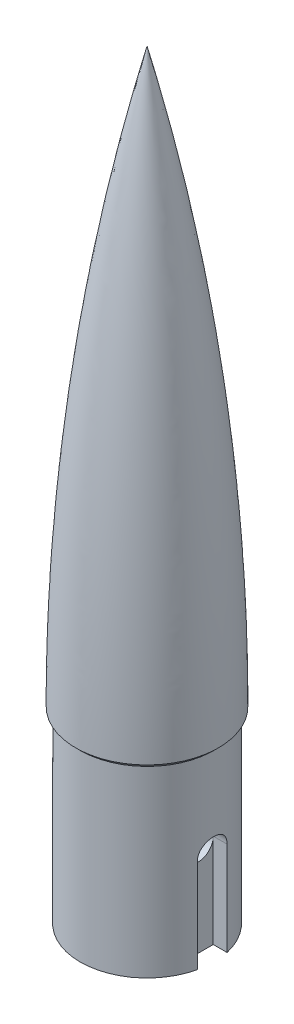
SolidWorks part; units mm, degrees
ref_plane "Front Plane" through (0, 0, 0) normal (0, 0, 1) x (1, 0, 0)
ref_plane "Top Plane" through (0, 0, 0) normal (0, 1, 0) x (1, 0, 0)
ref_plane "Right Plane" through (0, 0, 0) normal (1, 0, 0) x (0, 0, -1)
sketch "Sketch1" plane through (0, 0, 0) normal (0, 1, 0) x (1, 0, 0)
  circle A0 centre (0, 0) radius 8.895
  dimension "D1" = 17.79
extrude "Boss-Extrude1" add sketch "Sketch1" against normal blind 25
sketch "Sketch2" plane through (0, -25, 0) normal (0, -1, 0) x (1, 0, 0)
  line L0 (-6.8312, 1.9844) -> (-6.8312, -1.9844)
  line L1 (-6.8312, 1.9844) -> (-8.6708, 1.9844)
  line L2 (-6.8312, -1.9844) -> (-8.6708, -1.9844)
  line L3 (-8.895, 0) -> (-8.895, -1.1975) construction
  circle A0 centre (0, 0) radius 8.895 construction
  arc A1 (-8.6708, 1.9844) -> (-8.6708, -1.9844) centre (0, 0) ccw
  point P3 (-6.8313, 0)
  dimension "D2" = 3.9688
  dimension "D1" = 2.0637
extrude "Cut-Extrude1" cut sketch "Sketch2" against normal blind 12.5
mirror "Mirror1" about plane through (0, 0, 0) normal (1, 0, 0) of "Cut-Extrude1"
sketch "Sketch3" plane through (0, 0, 0) normal (1, 0, 0) x (0, 0, -1)
  line L0 (1.9844, -12.5) -> (-1.9844, -12.5) construction
  circle A0 centre (0, -12.5) radius 1.9844
extrude "Cut-Extrude2" cut sketch "Sketch3" against normal through all both and the other way through all
sketch "Sketch4" plane through (0, 0, 0) normal (0, 0, 1) x (1, 0, 0)
  line L0 (0, 0) -> (0, 76.2)
  line L1 (0, 0) -> (9.5, 0)
  arc A0 (9.5, 0) -> (0, 76.2) centre (-300.8521, 0) ccw
  dimension "D1" = 9.5
  dimension "D2" = 76.2
revolve "Revolve1" add sketch "Sketch4" angle 360 about L0
chamfer "Chamfer1" distance 0.6 angle 45 1 edges at (0, 0, 8.895)
equation "\"D_SHOULDER\"= 17.79mm"
equation "\"OD_AIRF\"= 19mm"
equation "\"W_CORD\"= 3.175mm"
equation "\"L_SHOULDER\"= 25mm"
equation "\"L_CONE\"= 3in"
equation "\"D1@Sketch1\"=\"D_SHOULDER\""
equation "\"D1@Boss-Extrude1\"=\"L_SHOULDER\""
equation "\"D2@Sketch2\"=1.25*\"W_CORD\""
equation "\"D1@Sketch2\"=0.65*\"W_CORD\""
equation "\"D1@Cut-Extrude1\"=\"L_SHOULDER\"/2"
equation "\"D1@Sketch4\"=\"OD_AIRF\"/2"
equation "\"D2@Sketch4\"=\"L_CONE\""
